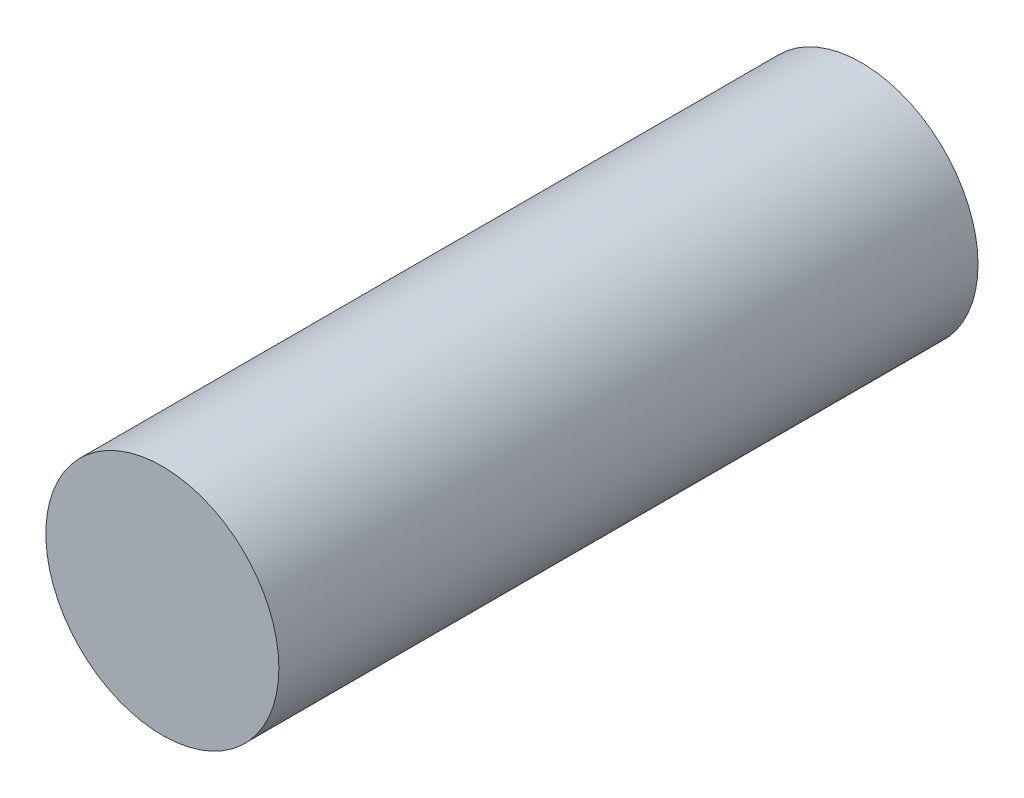
SolidWorks part; units mm, degrees
ref_plane "Спереди" through (0, 0, 0) normal (0, 0, 1) x (1, 0, 0)
ref_plane "Сверху" through (0, 0, 0) normal (0, 1, 0) x (1, 0, 0)
ref_plane "Справа" through (0, 0, 0) normal (1, 0, 0) x (0, 0, -1)
other "Configuration Table"
sketch "Sketch1" plane through (0, 0, 0) normal (0, 0, 1) x (1, 0, 0)
  circle A0 centre (0, 10.6109) radius 1
  dimension "D1" = 2
extrude "Boss-Extrude1" add sketch "Sketch1" along normal blind 6 contours A0
equation "\"R small\"= 2"
equation "\"R big\"= 4"
equation "\"width\"= 0.6"
equation "\"border width\"= 1"
equation "\"D1@Sketch1\"=\"R small\""
equation "\"depth\"= 3"
